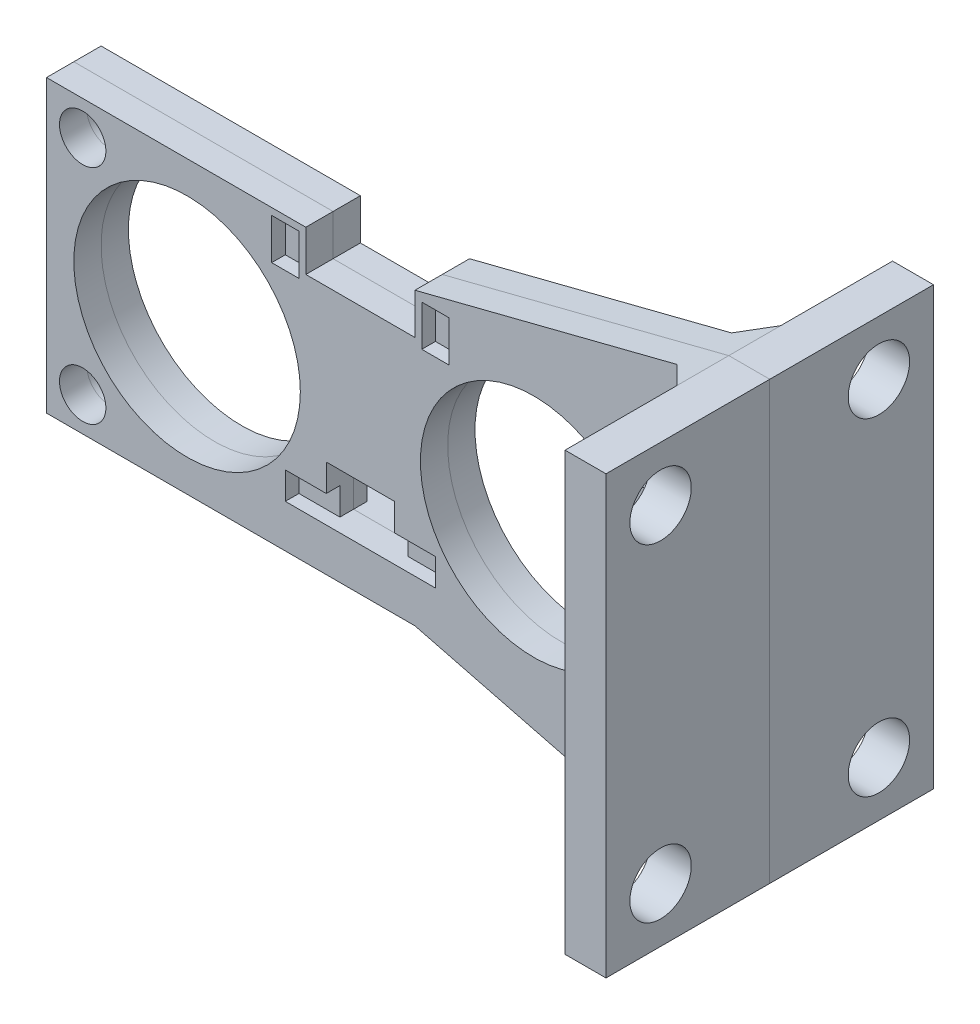
SolidWorks part; units mm, degrees
material "ABS"
ref_plane "前基準面" through (0, 0, 0) normal (0, 0, 1) x (1, 0, 0)
ref_plane "上基準面" through (0, 0, 0) normal (0, 1, 0) x (1, 0, 0)
ref_plane "右基準面" through (0, 0, 0) normal (1, 0, 0) x (0, 0, -1)
sketch "草圖1" plane through (0, 0, 0) normal (0, 0, 1) x (1, 0, 0)
  line L1 (-23, -10.65) -> (23, -10.65)
  line L2 (-23, -10.65) -> (-23, 10.65)
  line L3 (-23, 10.65) -> (23, 10.65)
  line L4 (23, -10.65) -> (23, 10.65)
  line L5 (-23, -10.65) -> (23, 10.65) construction
  line L6 (-23, 10.65) -> (23, -10.65) construction
  point P0 (0, 0)
  dimension "D1" = 46
  dimension "D2" = 21.3
extrude "填料-伸長1" add sketch "草圖1" along normal blind 2
sketch "草圖2" plane through (0, 0, 2) normal (0, 0, 1) x (1, 0, 0)
  line L0 (-12.7, 0) -> (12.7, 0) construction
  circle A0 centre (-12.7, 0) radius 8.3
  circle A1 centre (12.7, 0) radius 8.3
  point P4 (0, 0)
  dimension "D1" = 25.4
  dimension "D2" = 16.6
extrude "除料-伸長1" cut sketch "草圖2" against normal through all
sketch "草圖3" plane through (0, 0, 2) normal (0, 0, 1) x (1, 0, 0)
  line L0 (0, 0) -> (0, 9.15) construction
  line L1 (23, 10.65) -> (-23, 10.65) construction
  line L2 (-4, 7.65) -> (4, 7.65)
  line L3 (-4, 7.65) -> (-4, 10.65)
  line L4 (-4, 10.65) -> (4, 10.65)
  line L5 (4, 7.65) -> (4, 10.65)
  line L6 (-4, 7.65) -> (4, 10.65) construction
  line L7 (-4, 10.65) -> (4, 7.65) construction
  dimension "D1" = 8
  dimension "D2" = 3
extrude "除料-伸長2" cut sketch "草圖3" against normal through all
sketch "草圖4" plane through (0, 0, 2) normal (0, 0, 1) x (1, 0, 0)
  line L0 (0, 0) -> (0, -5.5) construction
  line L2 (-2.5, -3.5) -> (2.5, -3.5)
  line L3 (-2.5, -3.5) -> (-2.5, -7.5)
  line L4 (-2.5, -7.5) -> (2.5, -7.5)
  line L5 (2.5, -3.5) -> (2.5, -7.5)
  line L6 (-2.5, -3.5) -> (2.5, -7.5) construction
  line L7 (-2.5, -7.5) -> (2.5, -3.5) construction
  dimension "D1" = 5
  dimension "D2" = 4
  dimension "D3" = 5.5
extrude "除料-伸長3" cut sketch "草圖4" against normal through all
sketch "草圖5" plane through (0, 0, 2) normal (0, 0, 1) x (1, 0, 0)
  line L0 (0, 0) -> (0, 8.65) construction
  line L1 (2.5, -7.5) -> (5.5, -7.5)
  line L2 (2.5, -7.5) -> (2.5, -5.5)
  line L3 (2.5, -5.5) -> (5.5, -5.5)
  line L4 (5.5, -7.5) -> (5.5, -5.5)
  line L5 (-5.5, 8.65) -> (5.5, 8.65) construction
  line L6 (23, 10.65) -> (4, 10.65) construction
  line L7 (-4.5, 10.15) -> (-6.5, 10.15)
  line L8 (-4.5, 10.15) -> (-4.5, 7.15)
  line L9 (-4.5, 7.15) -> (-6.5, 7.15)
  line L10 (-6.5, 10.15) -> (-6.5, 7.15)
  line L11 (-4.5, 10.15) -> (-6.5, 7.15) construction
  line L12 (-4.5, 7.15) -> (-6.5, 10.15) construction
  line L13 (6.5, 10.15) -> (4.5, 10.15)
  line L14 (6.5, 10.15) -> (6.5, 7.15)
  line L15 (6.5, 7.15) -> (4.5, 7.15)
  line L16 (4.5, 10.15) -> (4.5, 7.15)
  line L17 (6.5, 10.15) -> (4.5, 7.15) construction
  line L18 (6.5, 7.15) -> (4.5, 10.15) construction
  line L20 (-2.5, -7.5) -> (-5.5, -7.5)
  line L21 (-2.5, -7.5) -> (-2.5, -5.5)
  line L22 (-2.5, -5.5) -> (-5.5, -5.5)
  line L23 (-5.5, -7.5) -> (-5.5, -5.5)
  point P10 (0, 8.65)
  dimension "D1" = 2
  dimension "D2" = 3
  dimension "D3" = 2
  dimension "D4" = 3
  dimension "D5" = 11
  dimension "D6" = 0.5
extrude "除料-伸長4" cut sketch "草圖5" against normal blind 1
hole_wizard "M3 餘隙孔1" positions "草圖6" profile "草圖7" hole size "M3" standard "Ansi Metric" end condition through all
sketch "草圖6" plane through (0, 0, 2) normal (0, 0, 1) x (1, 0, 0)
  line L1 (-20.35, -8.15) -> (20.35, -8.15) construction
  line L2 (-20.35, -8.15) -> (-20.35, 8.15) construction
  line L3 (-20.35, 8.15) -> (20.35, 8.15) construction
  line L4 (20.35, -8.15) -> (20.35, 8.15) construction
  line L5 (-20.35, -8.15) -> (20.35, 8.15) construction
  line L6 (-20.35, 8.15) -> (20.35, -8.15) construction
  point P1 (20.35, 8.15)
  point P112 (-20.35, -8.15)
  point P113 (-20.35, 8.15)
  point P114 (20.35, -8.15)
  point P118 (0, 0)
  dimension "D1" = 16.3
  dimension "D2" = 40.7
sketch "草圖7" plane through (20.35, 8.15, 2) normal (1, 0, 0) x (0, -1, 0)
  line L0 (0, 0) -> (0, 2)
  line L1 (0, 2) -> (1.7, 2)
  line L2 (1.7, 2) -> (1.7, 0)
  line L5 (1.7, 0) -> (0, 0)
  line L11 (0, -6.35) -> (0, 107.95) construction
  dimension "貫穿孔直徑" = 3.4
  dimension "貫穿孔深度" = 2
sketch "草圖13" plane through (23, 0, 0) normal (1, 0, 0) x (0, 0, -1)
  line L1 (-2, 10.65) -> (0, 10.65)
  line L2 (-2, 10.65) -> (-2, -10.65)
  line L3 (-2, -10.65) -> (0, -10.65)
  line L4 (0, 10.65) -> (0, -10.65)
extrude "填料-伸長5" add sketch "草圖13" along normal blind 2
sketch "草圖9" plane through (0, 0, 0) normal (0, 0, 1) x (1, 0, 0)
  line L1 (25, 16) -> (28, 16)
  line L2 (25, 16) -> (25, -16)
  line L3 (25, -16) -> (28, -16)
  line L4 (28, 16) -> (28, -16)
  line L6 (25, -10.65) -> (25, 10.65) construction
  point P9 (25, 0)
  dimension "D1" = 3
  dimension "D2" = 32
extrude "填料-伸長3" add sketch "草圖9" along normal blind 12
hole_wizard "M4 餘隙孔1" positions "草圖10" profile "草圖11" hole size "M4" standard "Ansi Metric" end condition through all
sketch "草圖10" plane through (25, 0, 0) normal (-1, 0, 0) x (0, 0, 1)
  line L0 (12, 0) -> (8, 0) construction
  line L1 (12, 16) -> (12, -16) construction
  line L4 (8, -12) -> (8, 12) construction
  point P7 (8, -12)
  point P8 (8, 12)
  dimension "D1" = 24
  dimension "D2" = 4
sketch "草圖11" plane through (25, 12, 8) normal (0, 1, 0) x (0, 0, 1)
  line L0 (0, 0) -> (0, 3)
  line L1 (0, 3) -> (2.25, 3)
  line L2 (2.25, 3) -> (2.25, 0)
  line L5 (2.25, 0) -> (0, 0)
  line L11 (0, -6.35) -> (0, 107.95) construction
  dimension "貫穿孔直徑" = 4.5
  dimension "貫穿孔深度" = 3
sketch "草圖12" plane through (0, 0, 0) normal (0, 0, 1) x (1, 0, 0)
  line L0 (25, 16) -> (4, 10.65)
  line L1 (4, 10.65) -> (25, 10.65)
  line L2 (25, 10.65) -> (25, 16)
extrude "填料-伸長4" add sketch "草圖12" along normal up to surface (2 mm away) up to face at (22.05, 8.15, 2)
mirror "鏡射1" about plane through (0, 0, 0) normal (0, 1, 0) of "填料-伸長4"
chamfer "導角1" distance 1.8 angle 45 1 edges at (25, 0, 2)
mirror "鏡射2" about plane through (0, 0, 0) normal (0, 0, 1) of bodies 111
split "分割1" trim tools "前基準面" bodies to split 114 111 resulting bodies 115 116
